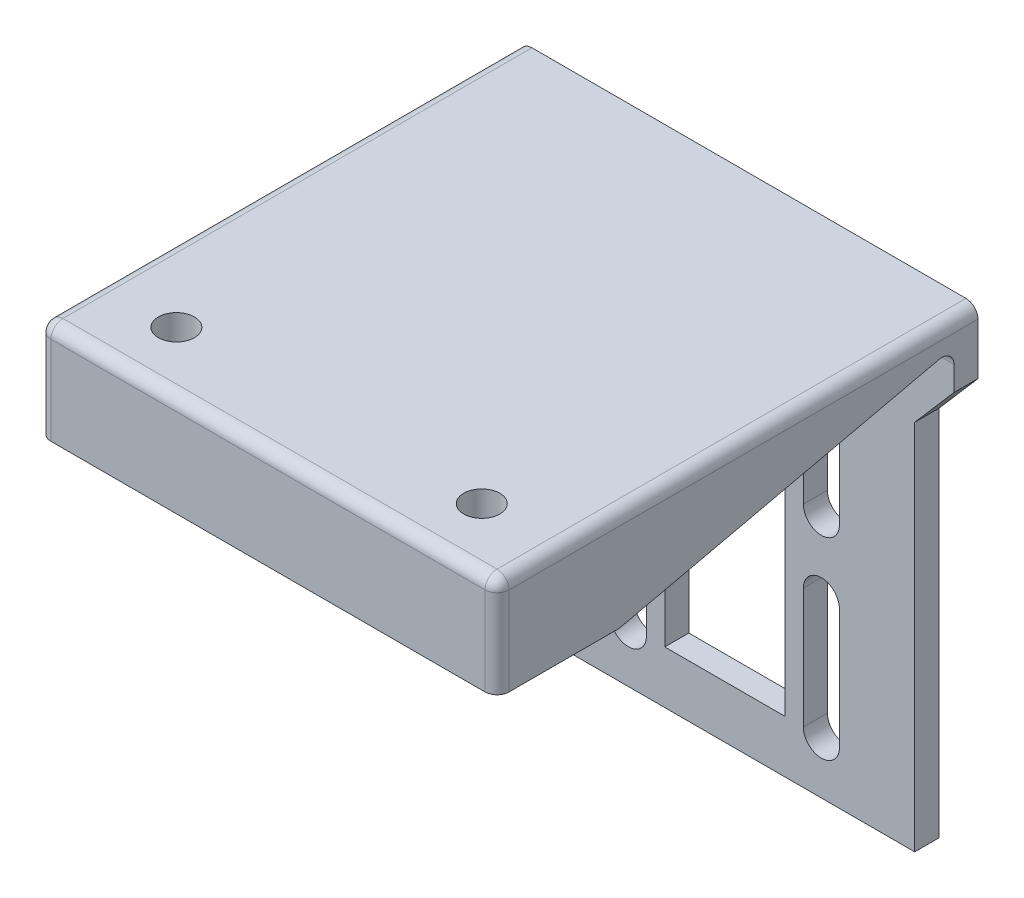
SolidWorks part; units mm, degrees
ref_plane "Front Plane" through (0, 0, 0) normal (0, 0, 1) x (1, 0, 0)
ref_plane "Top Plane" through (0, 0, 0) normal (0, 1, 0) x (1, 0, 0)
ref_plane "Right Plane" through (0, 0, 0) normal (1, 0, 0) x (0, 0, -1)
sketch "Sketch1" plane through (0, 0, 0) normal (1, 0, 0) x (0, 0, -1)
  line L1 (0, 0) -> (-2, 0)
  line L2 (0, 0) -> (0, 40)
  line L3 (0, 40) -> (-40, 40)
  line L4 (-40, 38) -> (-40, 40)
  line L7 (-40, 38) -> (-2, 38)
  line L8 (-2, 0) -> (-2, 38)
  dimension "D1" = 40
  dimension "D2" = 40
  dimension "D3" = 2
extrude "Boss-Extrude1" add sketch "Sketch1" along normal mid plane 38.1
sketch "Sketch2" plane through (0, 40, 0) normal (0, 1, 0) x (1, 0, 0)
  line L0 (12.7, -25.7242) -> (12.7, -14.2758) construction
  line L1 (11.15, -25.7242) -> (11.15, -14.2758)
  line L2 (14.25, -25.7242) -> (14.25, -14.2758)
  line L3 (0, 0) -> (0, -40) construction
  line L4 (19.05, 0) -> (-19.05, 0) construction
  line L5 (19.05, -40) -> (-19.05, -40) construction
  line L6 (-12.7, -25.7242) -> (-12.7, -14.2758) construction
  line L7 (-11.15, -25.7242) -> (-11.15, -14.2758)
  line L8 (-14.25, -25.7242) -> (-14.25, -14.2758)
  line L9 (12.7, -25.7242) -> (12.7, -40) construction
  line L10 (12.7, -14.2758) -> (12.7, 0) construction
  arc A0 (11.15, -25.7242) -> (14.25, -25.7242) centre (12.7, -25.7242) ccw
  arc A1 (14.25, -14.2758) -> (11.15, -14.2758) centre (12.7, -14.2758) ccw
  arc A2 (-11.15, -25.7242) -> (-14.25, -25.7242) centre (-12.7, -25.7242) cw
  arc A3 (-14.25, -14.2758) -> (-11.15, -14.2758) centre (-12.7, -14.2758) cw
  point P2 (12.7, -20)
  point P15 (-12.7, -20)
  dimension "D1" = 12.7
  dimension "D2" = 3.1
extrude "Cut-Extrude1" [suppressed] cut sketch "Sketch2" against normal mid plane 38.1
sketch "Sketch3" plane through (0, 0, 2) normal (0, 0, 1) x (1, 0, 0)
  line L0 (-8.025, 30.4195) -> (-8.025, 20.4195) construction
  line L1 (-6.525, 30.4195) -> (-6.525, 20.4195)
  line L2 (-9.525, 30.4195) -> (-9.525, 20.4195)
  line L3 (-8.025, 14.3695) -> (-8.025, 4.3695) construction
  line L4 (-6.525, 14.3695) -> (-6.525, 4.3695)
  line L5 (-9.525, 14.3695) -> (-9.525, 4.3695)
  line L6 (0, 0) -> (0, 38) construction
  line L7 (19.05, 38) -> (-19.05, 38) construction
  line L8 (5, 30.4195) -> (5, 4.3695)
  line L9 (5, 30.4195) -> (-5, 30.4195)
  line L10 (0, 30.4195) -> (0, 4.3695)
  line L11 (5, 4.3695) -> (-5, 4.3695)
  line L12 (-5, 30.4195) -> (-5, 4.3695)
  line L13 (8.025, 14.3695) -> (8.025, 4.3695) construction
  line L14 (6.525, 14.3695) -> (6.525, 4.3695)
  line L15 (9.525, 14.3695) -> (9.525, 4.3695)
  line L16 (8.025, 30.4195) -> (8.025, 20.4195) construction
  line L17 (6.525, 30.4195) -> (6.525, 20.4195)
  line L18 (9.525, 30.4195) -> (9.525, 20.4195)
  line L19 (-19.05, 34.716) -> (-15.7864, 30.9424)
  line L20 (-19.05, 38) -> (-19.05, 0) construction
  line L21 (-15.7864, 30.9424) -> (-15.7864, 0)
  line L22 (19.05, 0) -> (-19.05, 0) construction
  line L23 (-19.05, 34.716) -> (-19.05, 0)
  line L24 (-19.05, 0) -> (-15.7864, 0)
  line L25 (19.05, 34.716) -> (19.05, 0)
  line L26 (19.05, 34.716) -> (15.7864, 30.9424)
  line L27 (15.7864, 30.9424) -> (15.7864, 0)
  line L28 (19.05, 0) -> (15.7864, 0)
  arc A0 (-6.525, 30.4195) -> (-9.525, 30.4195) centre (-8.025, 30.4195) ccw
  arc A1 (-9.525, 20.4195) -> (-6.525, 20.4195) centre (-8.025, 20.4195) ccw
  arc A2 (-6.525, 14.3695) -> (-9.525, 14.3695) centre (-8.025, 14.3695) ccw
  arc A3 (-9.525, 4.3695) -> (-6.525, 4.3695) centre (-8.025, 4.3695) ccw
  arc A4 (6.525, 14.3695) -> (9.525, 14.3695) centre (8.025, 14.3695) cw
  arc A5 (9.525, 4.3695) -> (6.525, 4.3695) centre (8.025, 4.3695) cw
  arc A6 (6.525, 30.4195) -> (9.525, 30.4195) centre (8.025, 30.4195) cw
  arc A7 (9.525, 20.4195) -> (6.525, 20.4195) centre (8.025, 20.4195) cw
  point P2 (-8.025, 25.4195)
  point P7 (-8.025, 9.3695)
  point P30 (8.025, 9.3695)
  point P37 (8.025, 25.4195)
  line M5 (-19.05, 38) -> (-19.05, 0)
  line M6 (-19.05, 0) -> (19.05, 0)
  line M7 (19.05, 0) -> (19.05, 38)
  dimension "D1" = 3
  dimension "D2" = 16.05
  dimension "D3" = 10
  dimension "D4" = 8.025
  dimension "D5" = 5
extrude "Cut-Extrude2" cut sketch "Sketch3" against normal through all contours L11 L8 L9 L10 | L9 L12 L11 L10 | L2 A1 L1 A0 | L5 A3 L4 A2 | A7 L18 A6 L17 | A5 L15 A4 L14 | L21 L19 M5 M6 | L26 L27 M6 M7
sketch "Sketch4" plane through (19.05, 0, 0) normal (1, 0, 0) x (0, 0, -1)
  line L0 (-2, 38) -> (-29.84, 31.65)
  line L1 (-29.84, 31.65) -> (-40, 31.65)
  line L2 (-40, 31.65) -> (-40, 38)
  line L3 (-40, 38) -> (-2, 38)
  dimension "D1" = 10.16
  dimension "D2" = 6.35
extrude "Boss-Extrude2" add sketch "Sketch4" against normal up to surface (38.1 mm away) up to face at (-19.05, 37.572, 14)
sketch "Sketch5" plane through (0, 40, 0) normal (0, 1, 0) x (1, 0, 0)
  line L0 (-12.7, -34.92) -> (12.7, -34.92) construction
  line L1 (0, -34.92) -> (0, -40) construction
  line L2 (19.05, -40) -> (-19.05, -40) construction
  circle A0 centre (-12.7, -34.92) radius 1.5
  circle A1 centre (12.7, -34.92) radius 1.5
  dimension "D1" = 3
  dimension "D2" = 25.4
  dimension "D3" = 5.08
extrude "Cut-Extrude3" cut sketch "Sketch5" against normal up to surface (8.35 mm away) up to face at (0, 31.65, 34.92)
fillet "Fillet1" radius 1 7 edges at (-19.05, 40, 20) (19.05, 40, 20) (-19.05, 35.825, 40) (19.05, 35.825, 40) (0, 40, 40) (0, 31.65, 29.84) (0, 38, 2)
